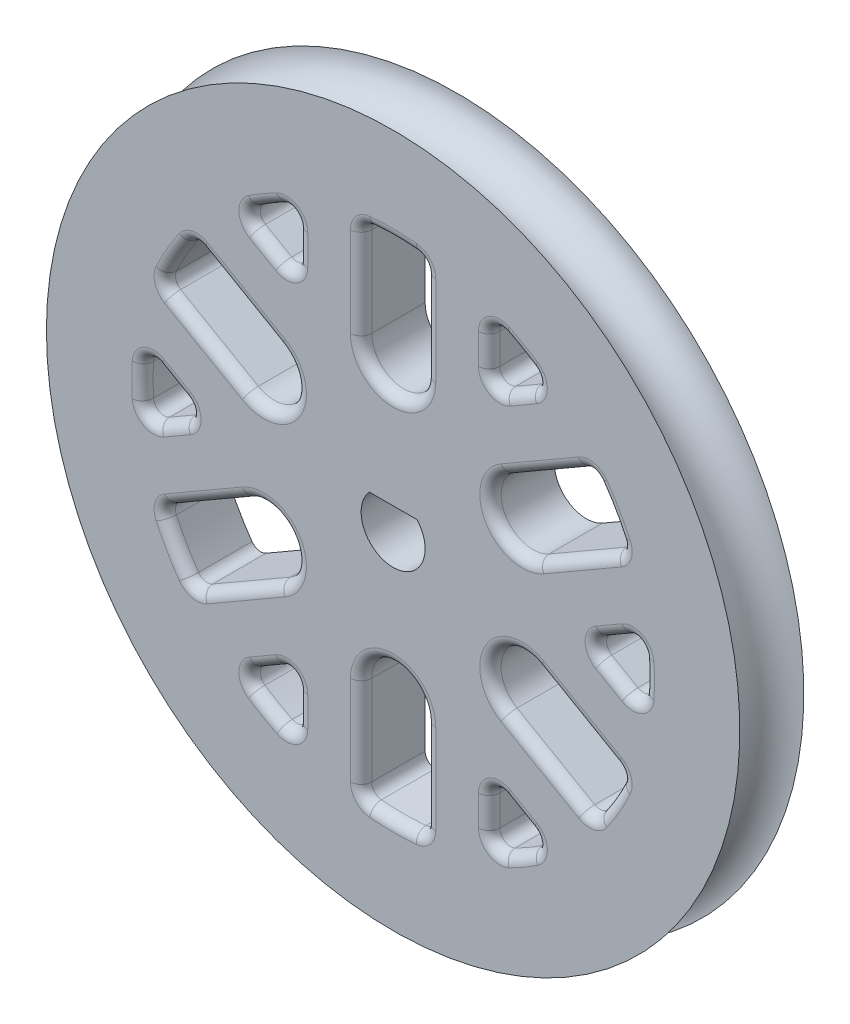
SolidWorks part; units mm, degrees
ref_plane "Front Plane" through (0, 0, 0) normal (0, 0, 1) x (1, 0, 0)
ref_plane "Top Plane" through (0, 0, 0) normal (0, 1, 0) x (1, 0, 0)
ref_plane "Right Plane" through (0, 0, 0) normal (1, 0, 0) x (0, 0, -1)
sketch "Sketch3" plane through (0, 0, 0) normal (0, 1, 0) x (1, 0, 0)
  line L0 (0, 1.5) -> (0, -1.5)
  line L1 (-16.25, 1.5) -> (0, 1.5)
  line L3 (0, -1.5) -> (-16.25, -1.5)
  line L4 (0, 1.5) -> (0, -1.5) construction
  arc A0 (-16.25, -1.5) -> (-16.25, 1.5) centre (-16.25, 0) ccw
  point P6 (0, 0)
  point P9 (0, 0)
  dimension "D1" = 1.5
  dimension "D2" = 32.5
revolve "Revolve1" add sketch "Sketch3" angle 360 about L0
sketch "Sketch6" plane through (0, 0, 1.5) normal (0, 0, 1) x (1, 0, 0)
  line L0 (-1.118, 1) -> (1.118, 1)
  arc A0 (-1.118, 1) -> (1.118, 1) centre (0, 0) ccw
  point P5 (0, -1.5)
  dimension "D1" = 3
  dimension "D2" = 2.5
extrude "Cut-Extrude2" cut sketch "Sketch6" against normal up to surface (3 mm away) up to face at (-16.25, 0, -1.5)
sketch "Sketch4" plane through (0, 0, 1.5) normal (0, 0, 1) x (1, 0, 0)
  line L7 (-1.5, 11.6539) -> (-1.5, 7)
  line L10 (1.5, 7) -> (1.5, 11.6539)
  line L11 (4.5, 10.8541) -> (4.5, 7.7942)
  line L12 (4.5, 7.7942) -> (7.15, 9.3242)
  line L13 (5.875, 10.1758) -> (0, 0) construction
  line L14 (0, 11.75) -> (0, 0) construction
  arc A5 (-1.5, 7) -> (1.5, 7) centre (0, 7) ccw
  arc A8 (1.5, 11.6539) -> (-1.5, 11.6539) centre (0, 0) ccw
  circle A9 centre (0, 0) radius 16.25 construction
  arc A10 (7.15, 9.3242) -> (4.5, 10.8541) centre (0, 0) ccw
  point P1 (0, 5.5)
  dimension "D1" = 5.5
  dimension "D3" = 3
  dimension "D4" = 30
  dimension "D5" = 3
  dimension "D2" = 4.5
extrude "Cut-Extrude1" cut sketch "Sketch4" against normal through all
fillet "Fillet2" radius 0.5 5 edges at (4.5, 7.7942, 0) (4.5, 10.8541, 0) (7.15, 9.3242, 0) (1.5, 11.6539, 0) (-1.5, 11.6539, 0)
fillet "Fillet3" radius 0.5 12 edges at (4.7365, 10.5027, 1.5) (5.875, 10.1758, 1.5) (6.7274, 9.3533, 1.5) (5.8638, 8.5816, 1.5) (4.75, 8.2272, 1.5) (-1.3689, 11.5429, 1.5) (0, 11.75, 1.5) (1.3689, 11.5429, 1.5) (1.5, 9.1027, 1.5) (0, 5.5, 1.5) (4.5, 9.369, 1.5) (-1.5, 9.1027, 1.5)
pattern_circular "CirPattern1" count 6 over 360 about axis through (0, 0, 0) along (0, 0, 1) of "Cut-Extrude1", "Fillet3", "Fillet2"
